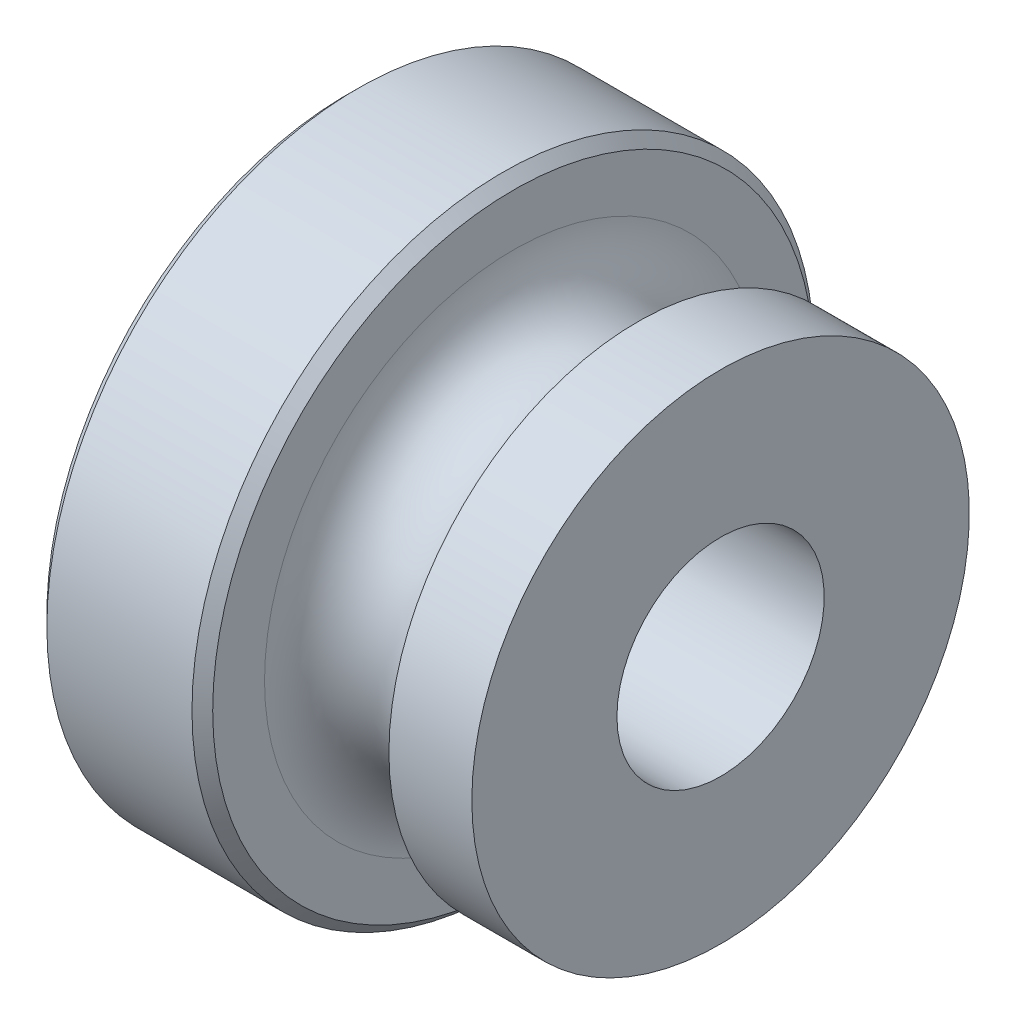
SolidWorks part; units mm, degrees
ref_plane "Front Plane" through (0, 0, 0) normal (0, 0, 1) x (1, 0, 0)
ref_plane "Top Plane" through (0, 0, 0) normal (0, 1, 0) x (1, 0, 0)
ref_plane "Right Plane" through (0, 0, 0) normal (1, 0, 0) x (0, 0, -1)
sketch "Sketch1" plane through (0, 0, 0) normal (0, 0, 1) x (1, 0, 0)
  line L0 (0, 0) -> (15.9098, 0) construction
  line L1 (0, 0) -> (0, 17.8789) construction
  line L2 (18, 12) -> (18, 5)
  line L3 (18, 5) -> (3, 5)
  line L4 (0, 10) -> (0, 15)
  line L5 (0, 15) -> (8, 15)
  line L6 (8, 15) -> (8, 12)
  line L7 (14, 12) -> (18, 12)
  line L8 (3, 5) -> (3, 7)
  arc A1 (8, 12) -> (14, 12) centre (11, 12) ccw
  arc A2 (3, 7) -> (0, 10) centre (0, 7) ccw
  point P6 (0, 0)
  point P14 (0, 0)
  dimension "D5" = 3
  dimension "D1" = 12
  dimension "D2" = 5
  dimension "D3" = 15
  dimension "D4" = 10
  dimension "D6" = 8
  dimension "D7" = 4
  dimension "D8" = 6
revolve "Revolve1" add sketch "Sketch1" angle 360 about L0
cosmetic thread "Cosmetic Thread1" parameters "D2"=12
chamfer "Chamfer1" distance 0.5 angle 45 2 edges at (8, 0, 15) (0, 0, 15)
sketch "Sketch2" plane through (0, 0, 0) normal (-1, 0, 0) x (0, 0, 1)
  circle A0 centre (0, 0) radius 15 construction
  circle A1 centre (0, 0) radius 15
